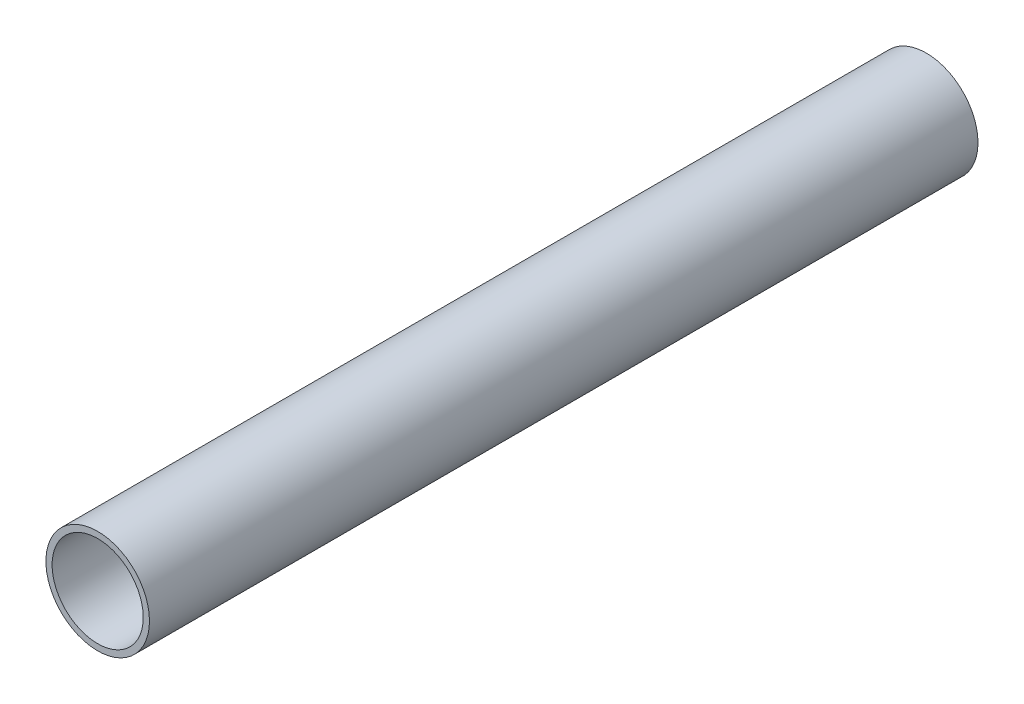
SolidWorks part; units mm, degrees
material "Carbon Fiber Tube - UD Approx"
ref_plane "Front Plane" through (0, 0, 0) normal (0, 0, 1) x (1, 0, 0)
ref_plane "Top Plane" through (0, 0, 0) normal (0, 1, 0) x (1, 0, 0)
ref_plane "Right Plane" through (0, 0, 0) normal (1, 0, 0) x (0, 0, -1)
sketch "Sketch1" plane through (0, 0, 0) normal (0, 0, 1) x (1, 0, 0)
  circle A0 centre (0, 0) radius 12.5
  circle A1 centre (0, 0) radius 11
  dimension "D1" = 25
  dimension "D2" = 22
extrude "Boss-Extrude1" add sketch "Sketch1" along normal blind 200
